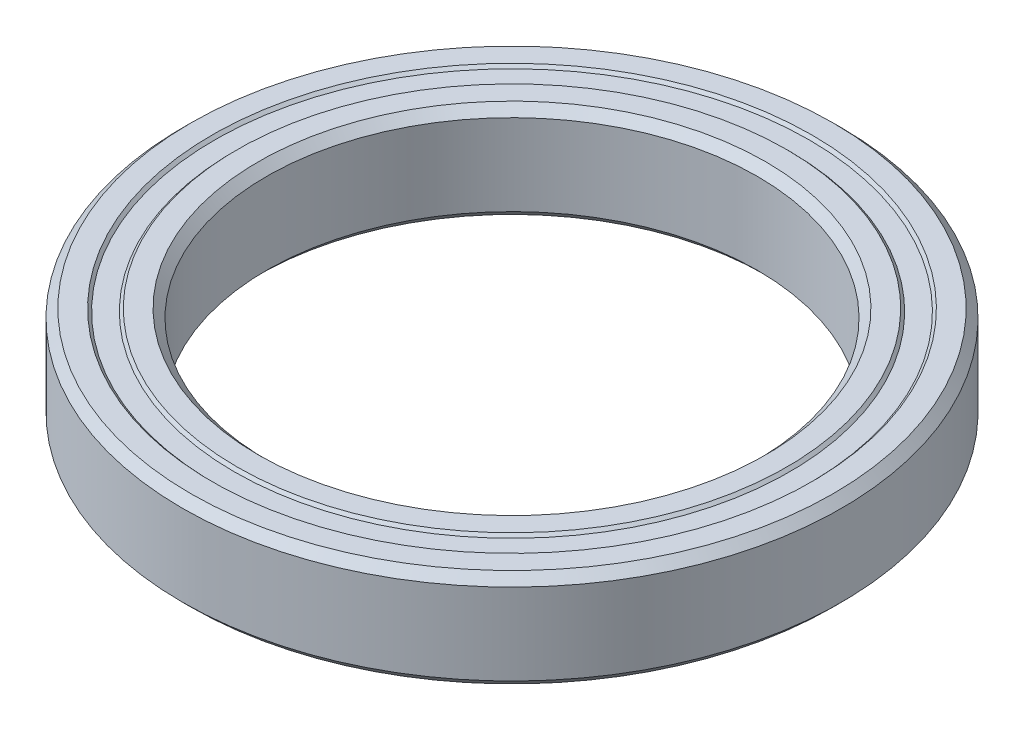
SolidWorks part; units mm, degrees
material "Stainless Steel (ferritic)"
ref_plane "Front Plane" through (0, 0, 0) normal (0, 0, 1) x (1, 0, 0)
ref_plane "Top Plane" through (0, 0, 0) normal (0, 1, 0) x (1, 0, 0)
ref_plane "Right Plane" through (0, 0, 0) normal (1, 0, 0) x (0, 0, -1)
sketch "Sketch1" plane through (0, 0, 0) normal (0, 0, 1) x (1, 0, 0)
  line L0 (0, -1.3494) -> (0, 70.5256) construction
  line L1 (17.5, 2.9) -> (17.5, -2.9)
  line L2 (17.5, -2.9) -> (18.1, -3.5)
  line L3 (18.1, -3.5) -> (19.6, -3.5)
  line L4 (19.6, -3.5) -> (19.8, -3.3)
  line L5 (19.8, -3.3) -> (21.2, -3.3)
  line L6 (21.2, -3.3) -> (21.4, -3.5)
  line L7 (21.4, -3.5) -> (22.9, -3.5)
  line L8 (22.9, -3.5) -> (23.5, -2.9)
  line L9 (23.5, -2.9) -> (23.5, 2.9)
  line L10 (23.5, 2.9) -> (22.9, 3.5)
  line L11 (22.9, 3.5) -> (21.4, 3.5)
  line L12 (21.4, 3.5) -> (21.2, 3.3)
  line L13 (21.2, 3.3) -> (19.8, 3.3)
  line L14 (19.8, 3.3) -> (19.6, 3.5)
  line L15 (19.6, 3.5) -> (18.1, 3.5)
  line L16 (18.1, 3.5) -> (17.5, 2.9)
  line L17 (0, 0) -> (17.5, 0) construction
  dimension "D1" = 17.5
  dimension "D2" = 7
  dimension "D3" = 0.6
  dimension "D4" = 0.2
  dimension "D5" = 23.5
  dimension "D6" = 1.5
revolve "Revolve1" add sketch "Sketch1" angle 360 about L0
